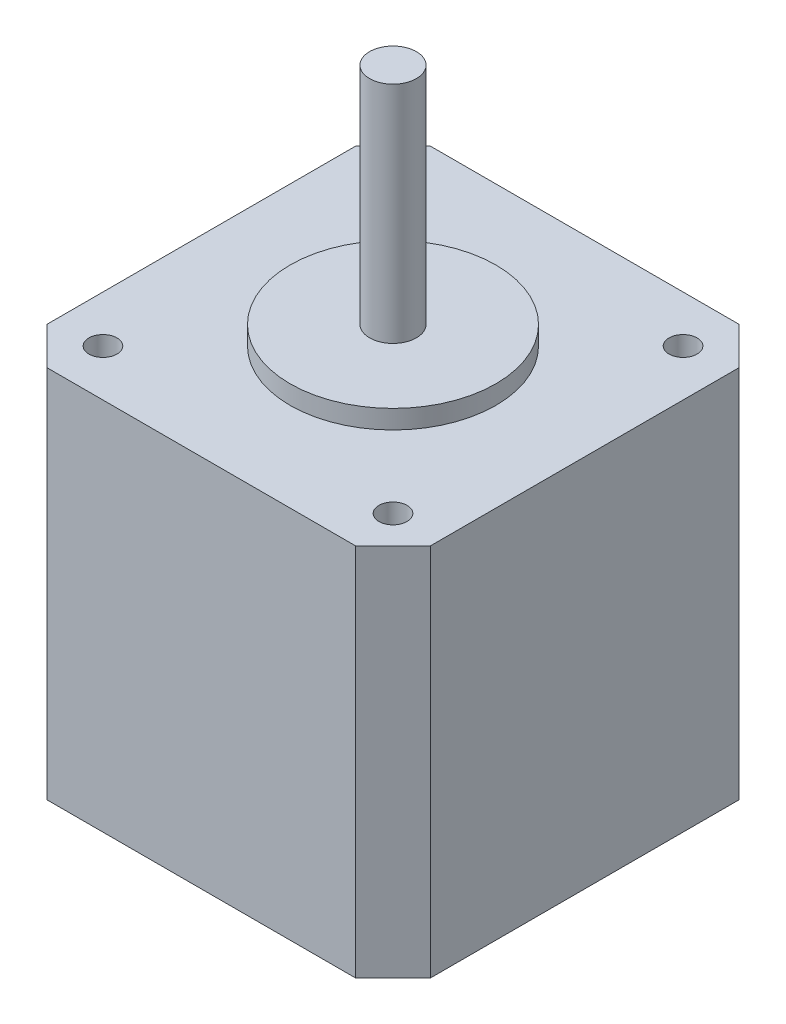
SolidWorks part; units mm, degrees
ref_plane "Front Plane" through (0, 0, 0) normal (0, 0, 1) x (1, 0, 0)
ref_plane "Top Plane" through (0, 0, 0) normal (0, 1, 0) x (1, 0, 0)
ref_plane "Right Plane" through (0, 0, 0) normal (1, 0, 0) x (0, 0, -1)
sketch "Sketch1" plane through (0, 0, 0) normal (0, 1, 0) x (1, 0, 0)
  line L0 (-16.5, 20.5) -> (-20.5, 16.5)
  line L1 (16.5, 20.5) -> (-16.5, 20.5)
  line L2 (20.5, 16.5) -> (20.5, -16.5)
  line L3 (16.5, -20.5) -> (-16.5, -20.5)
  line L4 (-20.5, 16.5) -> (-20.5, -16.5)
  line L5 (20.5, 20.5) -> (-20.5, -20.5) construction
  line L6 (20.5, -20.5) -> (-20.5, 20.5) construction
  line L7 (20.5, 16.5) -> (16.5, 20.5)
  line L8 (20.5, -16.5) -> (16.5, -20.5)
  line L9 (-16.5, -20.5) -> (-20.5, -16.5)
  point P0 (0, 0)
  dimension "D1" = 41
  dimension "D2" = 41
extrude "Boss-Extrude1" add sketch "Sketch1" along normal blind 40
sketch "Sketch2" plane through (0, 40, 0) normal (0, 1, 0) x (1, 0, 0)
  circle A0 centre (0, 0) radius 11
  dimension "D1" = 22
extrude "Boss-Extrude2" add sketch "Sketch2" along normal blind 2
sketch "Sketch3" plane through (0, 42, 0) normal (0, 1, 0) x (1, 0, 0)
  circle A0 centre (0, 0) radius 2.5
  dimension "D1" = 5
extrude "Boss-Extrude3" add sketch "Sketch3" along normal blind 24
sketch "Sketch4" plane through (0, 40, 0) normal (0, 1, 0) x (1, 0, 0)
  line L1 (15.5, 15.5) -> (-15.5, 15.5) construction
  line L2 (15.5, 15.5) -> (15.5, -15.5) construction
  line L3 (15.5, -15.5) -> (-15.5, -15.5) construction
  line L4 (-15.5, 15.5) -> (-15.5, -15.5) construction
  line L5 (15.5, 15.5) -> (-15.5, -15.5) construction
  line L6 (15.5, -15.5) -> (-15.5, 15.5) construction
  circle A0 centre (-15.5, 15.5) radius 1.5
  circle A1 centre (15.5, 15.5) radius 1.5
  circle A2 centre (15.5, -15.5) radius 1.5
  circle A3 centre (-15.5, -15.5) radius 1.5
  point P0 (0, 0)
  dimension "D3" = 3
  dimension "D4" = 3
  dimension "D5" = 3
  dimension "D6" = 3
  dimension "D1" = 31
  dimension "D2" = 31
extrude "Cut-Extrude1" cut sketch "Sketch4" against normal blind 5
